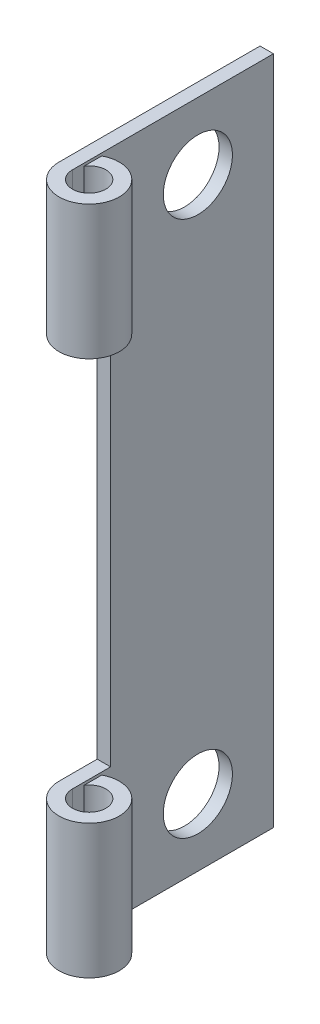
SolidWorks part; units mm, degrees
ref_plane "Front Plane" through (0, 0, 0) normal (0, 0, 1) x (1, 0, 0)
ref_plane "Top Plane" through (0, 0, 0) normal (0, 1, 0) x (1, 0, 0)
ref_plane "Right Plane" through (0, 0, 0) normal (1, 0, 0) x (0, 0, -1)
sketch "Sketch1" plane through (0, 0, 0) normal (1, 0, 0) x (0, 0, -1)
  line L0 (0, 0) -> (0, 31.75) construction
  line L1 (0, 0) -> (9.525, 0) construction
  line L2 (4.3053, 3.175) -> (7.5819, 3.175) construction
  line L3 (0, 0) -> (-9.525, 0) construction
  point P3 (5.9436, 3.175)
  point P5 (5.9436, 28.575)
  point P6 (0, 6.35)
  point P9 (-101.6, 31.75)
  point P10 (5.9436, 3.175)
  point P11 (-25.4, 31.75)
  point P12 (-127, 31.75)
  point P13 (-5.9436, 28.575)
  point P14 (-5.9436, 3.175)
  dimension "Knuckle Length" = 6.35
  dimension "Length Corner" = 3.175
  dimension "Height Corner" = 3.5814
  dimension "Overall Width" = 19.05
  dimension "Leaf Height" = 31.75
  dimension "MTG Dia" = 3.2766
  dimension "D1" = 3.175
  dimension "Num Holes" = 101.6
  dimension "Spring Knuckles" = 25.4
  dimension "Num Knuckles" = 127
  dimension "D2" = 3.5814
  dimension "Length Corner 2" = 3.175
  dimension "D4" = 3.175
sketch "Sketch2" plane through (0, 0, 0) normal (0, 1, 0) x (1, 0, 0)
  line L0 (0.635, 0) -> (2.2225, 0) construction
  line L1 (0, 9.525) -> (0.635, 9.525) construction
  line L2 (-0.6096, 9.3027) -> (0, 9.3027) construction
  line L3 (1.4288, 0.7937) -> (1.4288, 1.4287) construction
  line L5 (1.4288, 1.4287) -> (1.4288, 9.3027) construction
  circle A0 centre (1.4288, 0) radius 0.7938 construction
  point P9 (1.4288, 0.8191)
  point P10 (0.762, 9.3027)
  dimension "Leaf Thickness" = 0.635
  dimension "Pin Dia" = 1.5875
  dimension "Wire Dia" = 0.6096
  dimension "Spring Leg Length" = 7.874
  dimension "Bend Clearence" = 0.127
  dimension "D1" = 0.6096
  dimension "Open Close Offset" = 1.3716
sketch "Sketch3" plane through (0, 0, 0) normal (0, 1, 0) x (1, 0, 0)
  line L0 (0.635, 9.525) -> (0, 9.525)
  line L1 (0, 9.525) -> (0, 0)
  line L2 (0, 0) -> (0, 9.525) construction
  line L3 (0.635, 9.525) -> (0.635, 0)
  line L4 (0.762, 1.2636) -> (0.762, 0.4307)
  arc A0 (0, 0) -> (0.762, 1.2636) centre (1.4287, 0) ccw
  arc A1 (0.635, 0) -> (0.762, 0.4307) centre (1.4287, 0) ccw
extrude "Boss-Extrude1" add sketch "Sketch3" along normal up to vertex (31.75 mm away) up to point (0, 31.75, 0)
sketch "Sketch7" plane through (0, 0, 0) normal (1, 0, 0) x (0, 0, -1)
  line L0 (-1.8098, 38.1) -> (1.8097, 38.1)
  line L1 (-1.8098, 12.7) -> (1.8097, 12.7)
  line L2 (-1.8098, 12.7) -> (-1.8097, 6.35)
  line L3 (-1.8097, 6.35) -> (1.8098, 6.35)
  line L4 (1.8097, 12.7) -> (1.8098, 6.35)
  line L5 (-1.8098, 25.4) -> (1.8097, 25.4)
  line L6 (-1.8098, 25.4) -> (-1.8097, 19.05)
  line L7 (1.8097, 25.4) -> (1.8098, 19.05)
  line L8 (-1.8097, 19.05) -> (1.8098, 19.05)
  line L9 (-1.8098, 12.7) -> (-1.8098, 25.4) construction
  line L10 (-1.8098, 38.1) -> (-1.8097, 31.75)
  line L11 (1.8097, 38.1) -> (1.8098, 31.75)
  line L12 (-1.8097, 31.75) -> (1.8098, 31.75)
  point P5 (0, 6.35)
  dimension "D1" = 6.35
  dimension "D2" = 3.6195
  dimension "D4" = 12.7
  dimension "D3" = 3
extrude "Cut-Extrude2" cut sketch "Sketch7" along normal through all
sketch "Sketch8" plane through (0, 0, 0) normal (1, 0, 0) x (0, 0, -1)
  line L0 (-1.8097, 6.35) -> (1.8098, 6.35) construction
  line L1 (-1.8097, 6.35) -> (1.8098, 6.35)
  line L2 (-1.8097, 6.35) -> (-1.8098, 0)
  line L3 (-1.8098, 0) -> (1.8098, 0)
  line L4 (1.8098, 6.35) -> (1.8098, 0)
  line L5 (-1.8098, 12.7) -> (-1.8097, 6.35) construction
  line L6 (-1.8097, 19.05) -> (1.8098, 19.05)
  line L7 (-1.8097, 19.05) -> (-1.8098, 12.7)
  line L8 (-1.8098, 12.7) -> (1.8098, 12.7)
  line L9 (1.8098, 19.05) -> (1.8098, 12.7)
  line L10 (-1.8097, 6.35) -> (-1.8097, 19.05) construction
  line L11 (-1.8097, 31.75) -> (1.8098, 31.75)
  line L12 (-1.8097, 31.75) -> (-1.8098, 25.4)
  line L13 (-1.8098, 25.4) -> (1.8098, 25.4)
  line L14 (1.8098, 31.75) -> (1.8098, 25.4)
  dimension "D2" = 12.7
  dimension "D1" = 3
sketch "Sketch10" plane through (0, 0, 0) normal (1, 0, 0) x (0, 0, -1)
  line L1 (1.8098, 19.05) -> (-1.8097, 19.05)
  line L2 (1.8098, 19.05) -> (1.8098, 12.7)
  line L3 (1.8098, 12.7) -> (-1.8098, 12.7)
  line L4 (-1.8097, 19.05) -> (-1.8098, 12.7)
  line L5 (-1.8097, 6.35) -> (1.8098, 6.35) construction
  line L7 (0, 0) -> (0, 31.75) construction
  point P4 (0, 12.7)
  dimension "D1" = 6.35
  dimension "D2" = 12.7
extrude "Cut-Extrude4" cut sketch "Sketch10" along normal through all
sketch "Sketch9" plane through (0, 0, 0) normal (0, 1, 0) x (1, 0, 0)
  line L0 (0.635, 0) -> (2.2225, 0) construction
  circle A0 centre (1.4288, 0) radius 0.7938
ref_plane "Plane1" through (0, 13.0048, 0) normal (0, 1, 0) x (1, 0, 0)
ref_plane "Plane2" through (0, 18.7452, 0) normal (0, 1, 0) x (1, 0, 0)
ref_plane "Plane3" through (0, 0, -9.3027) normal (0, 0, 1) x (1, 0, 0)
sketch "Sketch15" plane through (0, 0, 0) normal (1, 0, 0) x (0, 0, -1)
  line L0 (4.3053, 3.175) -> (7.5819, 3.175) construction
  circle A0 centre (5.9436, 3.175) radius 1.6383
extrude "Cut-Extrude5" cut sketch "Sketch15" along normal through all
ref_plane "Mid Plane" through (0, 15.875, 0) normal (0, -1, 0) x (-1, 0, 0)
mirror "Mirror1" about plane through (0, 15.875, 0) normal (0, -1, 0) of "Cut-Extrude5"
equation "\"Num Knuckles\"=5"
equation "\"D1@Sketch7\"=\"Knuckle Length@Sketch1\""
equation "\"D2@Sketch7\" = ( 2 * \"Leaf Thickness@Sketch2\" ) + \"Pin Dia@Sketch2\" + ( .04 * \"Overall Width@Sketch1\" )"
equation "\"D4@Sketch7\"=\"Knuckle Length@Sketch1\"*2"
equation "\"D3@Sketch7\" = int ( \"Num Knuckles@Sketch1\" / 2 )  + 1"
equation "\"D2@Sketch8\"=\"D4@Sketch7\""
equation "\"D1@Sketch8\"=\"D3@Sketch7\""
equation "\"Spring Knuckles\"= 1"
equation "\"D1@Sketch10\"= \"Knuckle Length@Sketch1\" * \"Spring Knuckles@Sketch1\""
equation "\"D2@Sketch10\"=\"Knuckle Length@Sketch1\"*(\"Num Knuckles@Sketch1\"-\"Spring Knuckles@Sketch1\")/2"
equation "\"D1@Plane1\"=\"D2@Sketch10\"+(\"Wire Dia@Sketch2\"/2)"
equation "\"Num Holes\"=4"
equation "\"D1@Sketch1\"= \"Length Corner@Sketch1\""
equation "\"D1@Sketch2\"= \"Wire Dia@Sketch2\""
equation "\"Knuckle Length@Sketch1\"=\"Leaf Height@Sketch1\"/\"Num Knuckles@Sketch1\""
equation "\"D2@Sketch1\"=\"Height Corner@Sketch1\""
equation "\"D4@Sketch1\" = \"Length Corner 2@Sketch1\""
